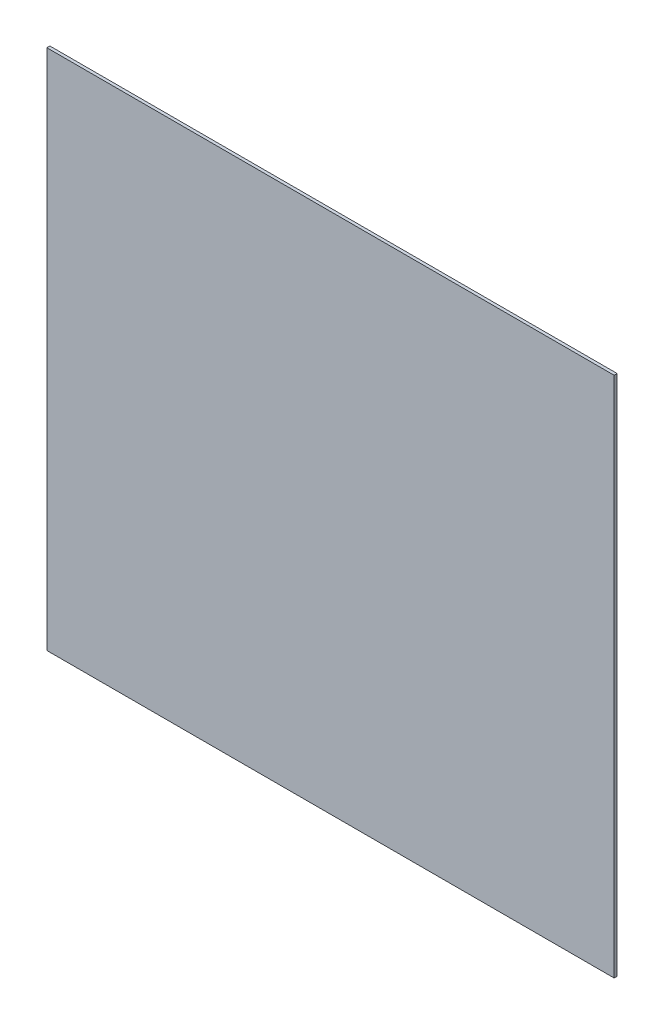
SolidWorks part; units mm, degrees
ref_plane "Přední rovina" through (0, 0, 0) normal (0, 0, 1) x (1, 0, 0)
ref_plane "Horní rovina" through (0, 0, 0) normal (0, 1, 0) x (1, 0, 0)
ref_plane "Pravá rovina" through (0, 0, 0) normal (1, 0, 0) x (0, 0, -1)
sketch "Skica1" plane through (0, 0, 0) normal (0, 0, 1) x (1, 0, 0)
  line L1 (-282.5, 260) -> (282.5, 260)
  line L2 (-282.5, 260) -> (-282.5, -260)
  line L3 (-282.5, -260) -> (282.5, -260)
  line L4 (282.5, 260) -> (282.5, -260)
  line L5 (-282.5, 260) -> (282.5, -260) construction
  line L6 (-282.5, -260) -> (282.5, 260) construction
  point P0 (0, 0)
  dimension "D1" = 565
  dimension "D2" = 520
extrude "Přidat vysunutím1" add sketch "Skica1" along normal blind 3
